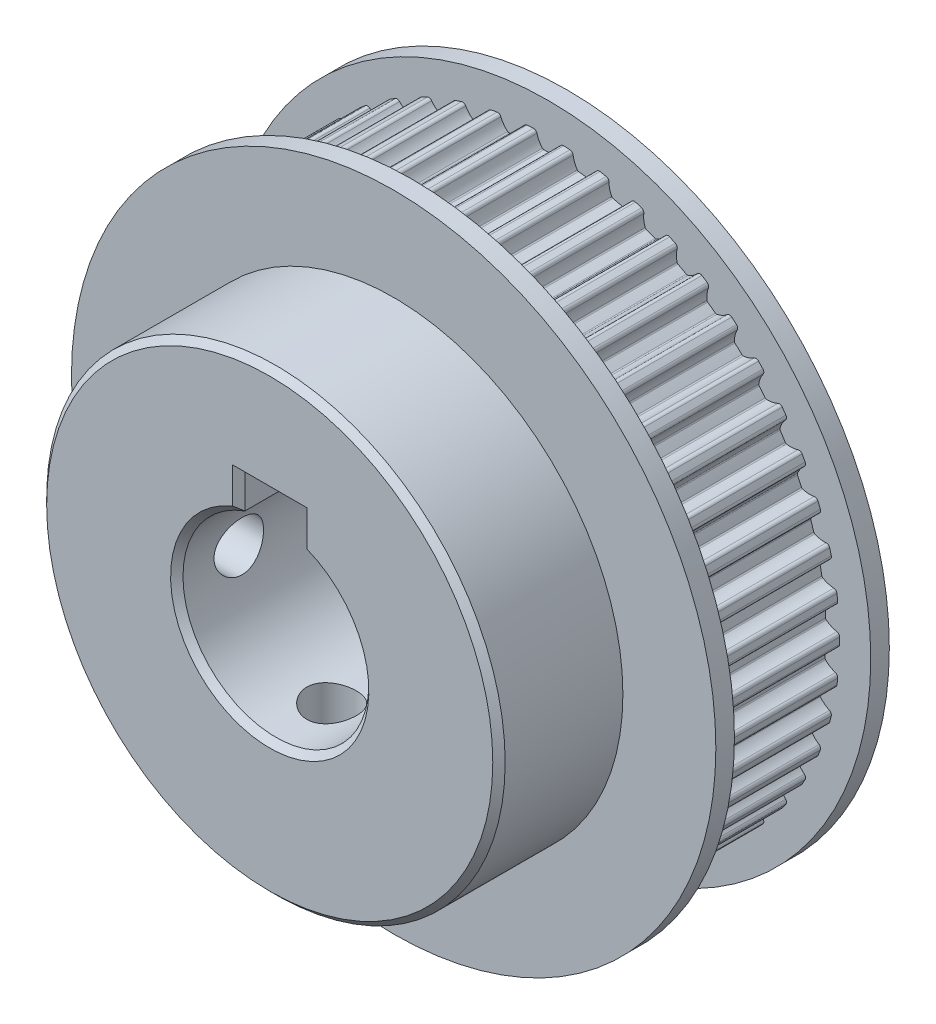
SolidWorks part; units mm, degrees
material "6061-T6 (SS)"
ref_plane "前基準面" through (0, 0, 0) normal (0, 0, 1) x (1, 0, 0)
ref_plane "上基準面" through (0, 0, 0) normal (0, 1, 0) x (1, 0, 0)
ref_plane "右基準面" through (0, 0, 0) normal (1, 0, 0) x (0, 0, -1)
sketch "草圖1" plane through (0, 0, 0) normal (0, 0, 1) x (1, 0, 0)
  circle A0 centre (0, 0) radius 23.49
  dimension "D1" = 46.98
extrude "填料-伸長1" add sketch "草圖1" along normal mid plane 11
sketch "草圖2" plane through (0, 0, 5.5) normal (0, 0, 1) x (1, 0, 0)
  line L0 (0, 0) -> (0, 23.49) construction
  line L1 (0, 23.49) -> (0, 23.744) construction
  line L2 (-0.975, 23.744) -> (0.975, 23.744) construction
  circle A0 centre (0, 0) radius 23.49 construction
  arc A1 (-0.3822, 22.3767) -> (0.3822, 22.3767) centre (0, 0) cw
  arc A2 (-0.3822, 22.3767) -> (-0.4965, 22.4267) centre (-0.3847, 22.5267) cw
  arc A3 (-0.4965, 22.4267) -> (-0.9369, 23.2488) centre (0.975, 23.744) cw
  arc A4 (-1.2225, 23.4582) -> (-0.9369, 23.2488) centre (-1.208, 23.1785) cw
  arc A5 (0.3822, 22.3767) -> (0.4965, 22.4267) centre (0.3847, 22.5267) ccw
  arc A6 (0.4965, 22.4267) -> (0.9369, 23.2488) centre (-0.975, 23.744) ccw
  arc A7 (1.2225, 23.4582) -> (0.9369, 23.2488) centre (1.208, 23.1785) ccw
  arc A8 (-1.2225, 23.4582) -> (1.2225, 23.4582) centre (0, 0) cw
  dimension "D1" = 0.15
  dimension "D2" = 1.975
  dimension "D3" = 0.28
  dimension "D4" = 1.11
  dimension "D5" = 0.254
  dimension "D6" = 1.95
extrude "除料-伸長1" cut sketch "草圖2" against normal through all and the other way through all
pattern_circular "環狀複製排列1" count 50 over 360 about axis through (0, 0, 0) along (0, 0, 1) of "除料-伸長1"
sketch "草圖3" plane through (0, 0, 5.5) normal (0, 0, 1) x (1, 0, 0)
  circle A0 centre (0, 0) radius 26
  dimension "D1" = 52
extrude "填料-伸長2" add sketch "草圖3" along normal blind 1.5
sketch "草圖9" plane through (0, 0, -5.5) normal (0, 0, -1) x (-1, 0, 0)
  circle A0 centre (0, 0) radius 26
  circle A1 centre (0, 0) radius 26 construction
extrude "填料-伸長3" add sketch "草圖9" along normal blind 1.5
sketch "草圖12" plane through (0, 0, 7) normal (0, 0, 1) x (1, 0, 0)
  circle A0 centre (0, 0) radius 18.5
  dimension "D1" = 37
extrude "填料-伸長4" add sketch "草圖12" along normal blind 10
sketch "草圖4" plane through (0, 0, 7) normal (0, 0, 1) x (1, 0, 0)
  circle A0 centre (0, 0) radius 7.5
  dimension "D1" = 15
extrude "除料-伸長2" cut sketch "草圖4" against normal through all and the other way through all
sketch "草圖13" plane through (0, 0, 17) normal (0, 0, 1) x (1, 0, 0)
  line L0 (0, 7.0711) -> (0, 0) construction
  line L1 (-2.5, 9.8) -> (2.5, 9.8)
  line L2 (-2.5, 9.8) -> (-2.5, 7.0711)
  line L3 (-2.5, 7.0711) -> (2.5, 7.0711)
  line L4 (2.5, 9.8) -> (2.5, 7.0711)
  line L5 (-2.5, 9.8) -> (2.5, 7.0711) construction
  line L6 (-2.5, 7.0711) -> (2.5, 9.8) construction
  line L7 (0, 7.5) -> (0, 9.8) construction
  circle A0 centre (0, 0) radius 7.5 construction
  point P0 (0, 8.4355)
  dimension "D2" = 2.3
  dimension "D1" = 5
extrude "除料-伸長5" cut sketch "草圖13" against normal through all
sketch "草圖10" plane through (0, 0, 0) normal (0, 1, 0) x (1, 0, 0)
  line L0 (0, 0) -> (0, -12) construction
  circle A0 centre (0, -12) radius 2
  dimension "D1" = 4
  dimension "D2" = 12
extrude "除料-伸長3" cut sketch "草圖10" against normal through all
chamfer "導角1" distance 0.5 angle 45 9 edges at (18.5, 0, 17) (0, -7.5, -7) (0, -7.5, 17) (-2.5, 8.4355, -7) (0, 9.8, -7) (2.5, 8.4355, -7) (2.5, 8.4355, 17) (0, 9.8, 17) (-2.5, 8.4355, 17)
pattern_circular "環狀複製排列2" count 2 over 90 about axis through (0, 0, 7) along (0, 0, -1) of "除料-伸長3"
